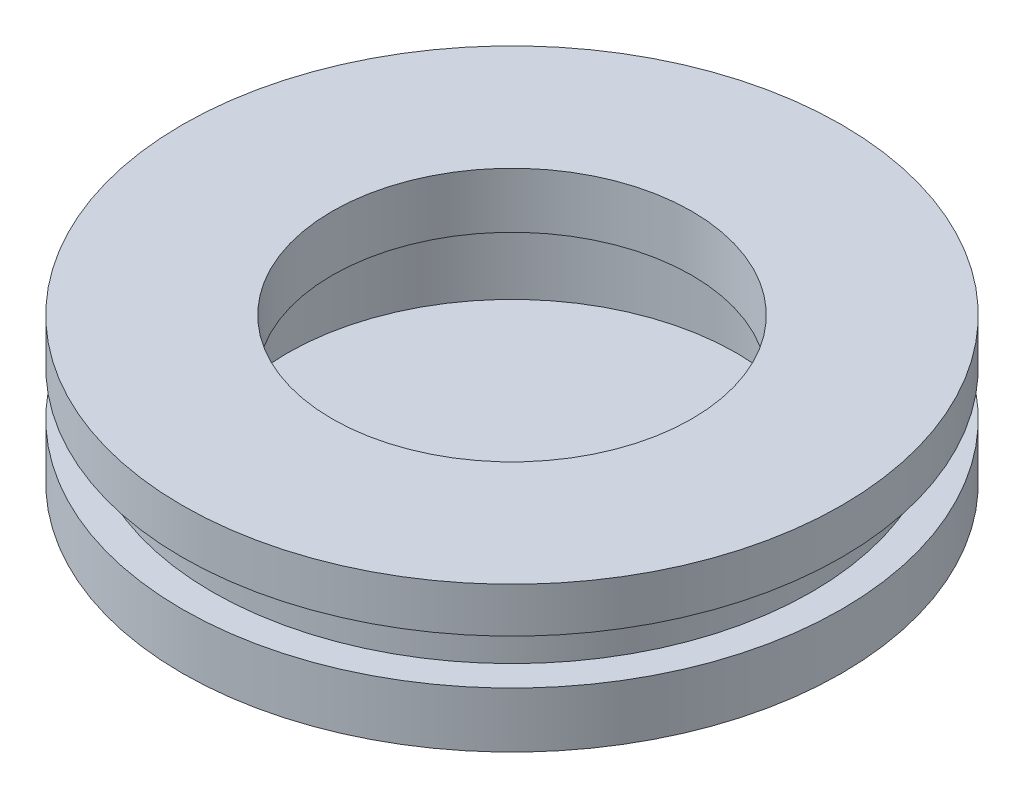
SolidWorks part; units mm, degrees
ref_plane "Front Plane" through (0, 0, 0) normal (0, 0, 1) x (1, 0, 0)
ref_plane "Top Plane" through (0, 0, 0) normal (0, 1, 0) x (1, 0, 0)
ref_plane "Right Plane" through (0, 0, 0) normal (1, 0, 0) x (0, 0, -1)
sketch "Sketch2" plane through (0, 0, 0) normal (0, 0, 1) x (1, 0, 0)
  line L0 (0, 0) -> (0, 8.8537)
  line L1 (0, 8.8537) -> (-11, 8.8537)
  line L2 (-11, 8.8537) -> (-11, 7.3537)
  line L3 (-11, 7.3537) -> (-10, 7.3537)
  line L4 (-10, 7.3537) -> (-10, 5.8537)
  line L5 (-10, 5.8537) -> (-11, 5.8537)
  line L6 (-11, 5.8537) -> (-11, 4.0037)
  line L7 (-11, 4.0037) -> (0, 0)
  dimension "D1" = 11
  dimension "D2" = 1.5
  dimension "D3" = 10
  dimension "D4" = 1.85
  dimension "D5" = 1.5
  dimension "D6" = 20
  dimension "D7" = 11
revolve "Revolve1" add sketch "Sketch2" angle 360 about L0
sketch "Sketch3" plane through (0, 0, 0) normal (0, 0, 1) x (1, 0, 0)
  line L0 (0, 0) -> (0, 4.0037)
  line L1 (11, 4.0037) -> (-11, 4.0037) construction
  line L2 (0, 4.0037) -> (0, 10.0037)
  line L3 (0, 10.0037) -> (-6, 10.0037)
  line L4 (-6, 10.0037) -> (-6, 7.0037)
  line L5 (-6, 7.0037) -> (-7.5, 7.0037)
  line L6 (-7.5, 7.0037) -> (-7.5, 4.0037)
  line L7 (-7.5, 4.0037) -> (0, 4.0037)
  dimension "D1" = 6
  dimension "D2" = 7.5
  dimension "D3" = 3
  dimension "D4" = 3
revolve "Cut-Revolve1" cut sketch "Sketch3" angle 360 about L2
